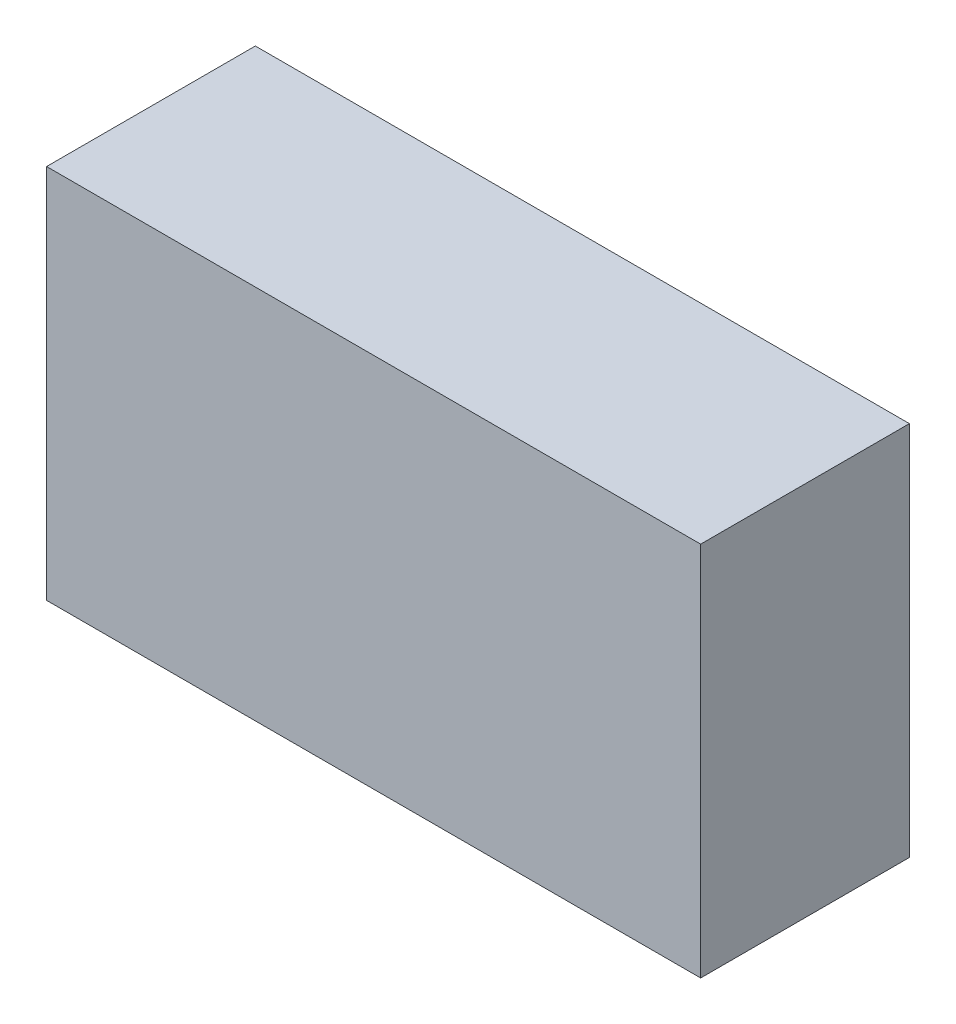
SolidWorks part; units mm, degrees
ref_plane "Front Plane" through (0, 0, 0) normal (0, 0, 1) x (1, 0, 0)
ref_plane "Top Plane" through (0, 0, 0) normal (0, 1, 0) x (1, 0, 0)
ref_plane "Right Plane" through (0, 0, 0) normal (1, 0, 0) x (0, 0, -1)
sketch "Эскиз1" plane through (0, 0, 0) normal (0, 0, 1) x (1, 0, 0)
  line L1 (-23.5, -13.5) -> (23.5, -13.5)
  line L2 (-23.5, -13.5) -> (-23.5, 13.5)
  line L3 (-23.5, 13.5) -> (23.5, 13.5)
  line L4 (23.5, -13.5) -> (23.5, 13.5)
  line L5 (-23.5, -13.5) -> (23.5, 13.5) construction
  line L6 (-23.5, 13.5) -> (23.5, -13.5) construction
  point P0 (0, 0)
  dimension "D1" = 27
  dimension "D2" = 47
extrude "Бобышка-Вытянуть1" add sketch "Эскиз1" along normal mid plane 15
